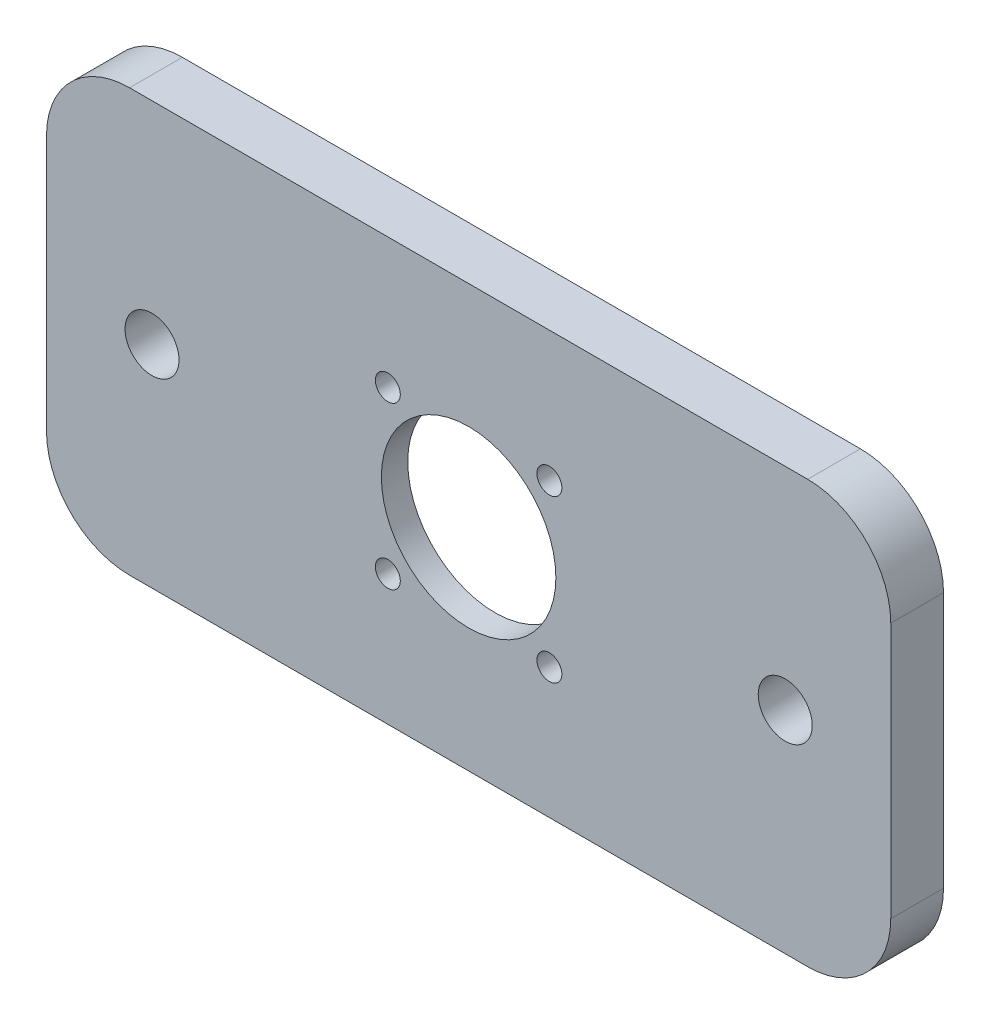
SolidWorks part; units mm, degrees
ref_plane "Front Plane" through (0, 0, 0) normal (0, 0, 1) x (1, 0, 0)
ref_plane "Top Plane" through (0, 0, 0) normal (0, 1, 0) x (1, 0, 0)
ref_plane "Right Plane" through (0, 0, 0) normal (1, 0, 0) x (0, 0, -1)
sketch "Sketch1" plane through (0, 0, 0) normal (0, 0, 1) x (1, 0, 0)
  line L0 (0, -0.2375) -> (0, 18.3505) construction
  line L1 (-50.8, -25.6375) -> (50.8, -25.6375)
  line L2 (-50.8, -25.6375) -> (-50.8, 25.1625)
  line L3 (-50.8, 25.1625) -> (50.8, 25.1625)
  line L4 (50.8, -25.6375) -> (50.8, 25.1625)
  line L5 (-50.8, -25.6375) -> (50.8, 25.1625) construction
  line L6 (-50.8, 25.1625) -> (50.8, -25.6375) construction
  line L7 (0, -0.2375) -> (-14.8193, -0.2375) construction
  circle A0 centre (0, -0.2375) radius 10.5
  circle A2 centre (-9.72, 9.4825) radius 1.5
  circle A3 centre (9.72, 9.4825) radius 1.5
  circle A4 centre (9.72, -9.9575) radius 1.5
  circle A5 centre (-9.72, -9.9575) radius 1.5
  point P20 (-11.8939, -0.2375)
  dimension "D3" = 3
  dimension "D4" = 3
  dimension "D5" = 3
  dimension "D6" = 3
  dimension "D7" = 21
  dimension "D9" = 9.72
  dimension "D10" = 9.72
  dimension "D11" = 9.72
  dimension "D1" = 101.6
  dimension "D2" = 50.8
  dimension "D8" = 9.72
extrude "Boss-Extrude1" add sketch "Sketch1" along normal blind 6.35
sketch "Sketch2" plane through (0, 0, 0) normal (0, 0, -1) x (-1, 0, 0)
  circle A0 centre (0, 0) radius 21
  dimension "D1" = 42
extrude "Cut-Extrude1" cut sketch "Sketch2" against normal blind 3.175
sketch "Sketch3" plane through (0, 0, 6.35) normal (0, 0, 1) x (1, 0, 0)
  line L0 (0, 0) -> (0, 17.528) construction
  line L1 (-50.8, -25.6375) -> (50.8, -25.6375) construction
  line L2 (-50.8, 25.1625) -> (-50.8, -25.6375) construction
  circle A0 centre (-38.1, -0.2375) radius 3.25
  circle A1 centre (38.1, -0.2375) radius 3.25
  dimension "D1" = 6.5
  dimension "D2" = 25.4
  dimension "D3" = 12.7
extrude "Cut-Extrude2" cut sketch "Sketch3" against normal through all
fillet "Fillet1" radius 10 4 edges at (50.8, 25.1625, 3.175) (50.8, -25.6375, 3.175) (-50.8, -25.6375, 3.175) (-50.8, 25.1625, 3.175)
sketch "Sketch4" [suppressed] plane through (0, 0, 0) normal (0, 0, -1) x (-1, 0, 0)
  line L0 (-40.8, 25.1625) -> (40.8, 25.1625) construction
  line L1 (0, 25.1625) -> (25.4, 25.1625)
  line L2 (0, 25.1625) -> (0, 50.5625)
  line L3 (0, 50.5625) -> (25.4, 50.5625)
  line L4 (25.4, 25.1625) -> (25.4, 50.5625)
  dimension "D1" = 25.4
  dimension "D2" = 25.4
